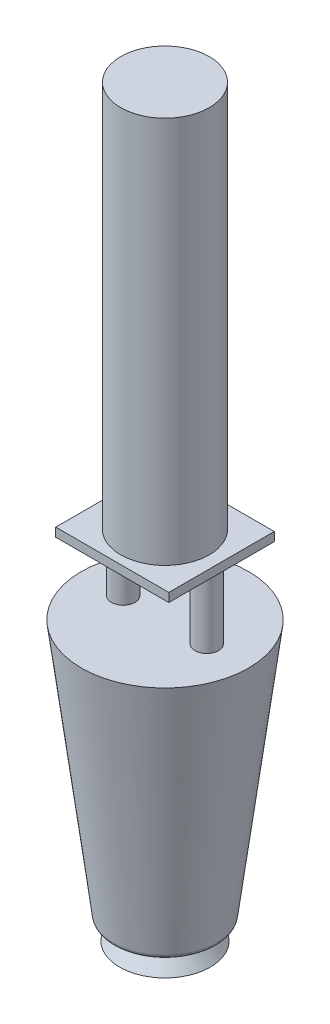
SolidWorks part; units mm, degrees
ref_plane "Front Plane" through (0, 0, 0) normal (0, 0, 1) x (1, 0, 0)
ref_plane "Top Plane" through (0, 0, 0) normal (0, 1, 0) x (1, 0, 0)
ref_plane "Right Plane" through (0, 0, 0) normal (1, 0, 0) x (0, 0, -1)
sketch "Sketch1" plane through (0, 0, 0) normal (0, 0, 1) x (1, 0, 0)
  line L0 (0, 0) -> (0, 63.2)
  line L1 (0, 63.2) -> (19, 63.2)
  line L2 (19, 63.2) -> (11.5884, 4.5553)
  line L3 (11.5884, 4.5553) -> (6.6275, 4.5553)
  line L4 (6.6275, 4.5553) -> (10.3082, 0)
  line L5 (10.3082, 0) -> (0, 0)
  line L6 (0, 0) -> (0, 66.166) construction
  dimension "D1" = 63.2
  dimension "D2" = 19
revolve "Revolve1" add sketch "Sketch1" angle 360 about L6
fillet "Fillet3" radius 1 1 edges at (0, 4.5553, -11.5884)
sketch "Sketch2" plane through (0, 0, 0) normal (0, 0, 1) x (1, 0, 0)
  line L0 (12.1621, 63.2) -> (12.1621, 79)
  line L1 (19, 63.2) -> (-19, 63.2) construction
  line L5 (9.4888, 63.2) -> (9.4888, 84.7068) construction
  line L6 (12.1621, 79) -> (9.4888, 79)
  line L7 (9.4888, 79) -> (9.4888, 63.2)
  line L8 (9.4888, 63.2) -> (12.1621, 63.2)
  dimension "D1" = 15.8
revolve "Revolve2" add sketch "Sketch2" angle 360 about L5
mirror "Mirror1" about plane through (0, 0, 0) normal (1, 0, 0) of "Revolve2"
sketch "Sketch4" plane through (0, 79, 0) normal (0, 1, 0) x (1, 0, 0)
  line L5 (-12.8453, -11.9793) -> (12.8453, -11.9793)
  line L6 (-12.8453, -11.9793) -> (-12.8453, 11.9793)
  line L7 (-12.8453, 11.9793) -> (12.8453, 11.9793)
  line L8 (12.8453, -11.9793) -> (12.8453, 11.9793)
  line L9 (0, 11.9793) -> (0, -11.9793) construction
  line L10 (-12.8453, 0) -> (12.8453, 0) construction
  point P0 (0, 0)
extrude "Boss-Extrude1" add sketch "Sketch4" along normal blind 2
sketch "Sketch5" plane through (0, 0, 0) normal (0, 0, 1) x (1, 0, 0)
  line L0 (0, 81) -> (0, 169)
  line L1 (-12.8453, 81) -> (12.8453, 81) construction
  line L2 (0, 169) -> (10.0571, 169)
  line L3 (10.0571, 169) -> (10.0571, 81)
  line L4 (10.0571, 81) -> (0, 81)
  line L5 (0, 81) -> (0, 182.6656) construction
  dimension "D1" = 88
  dimension "D2" = 10.0571
revolve "Revolve4" add sketch "Sketch5" angle 360 about L5
